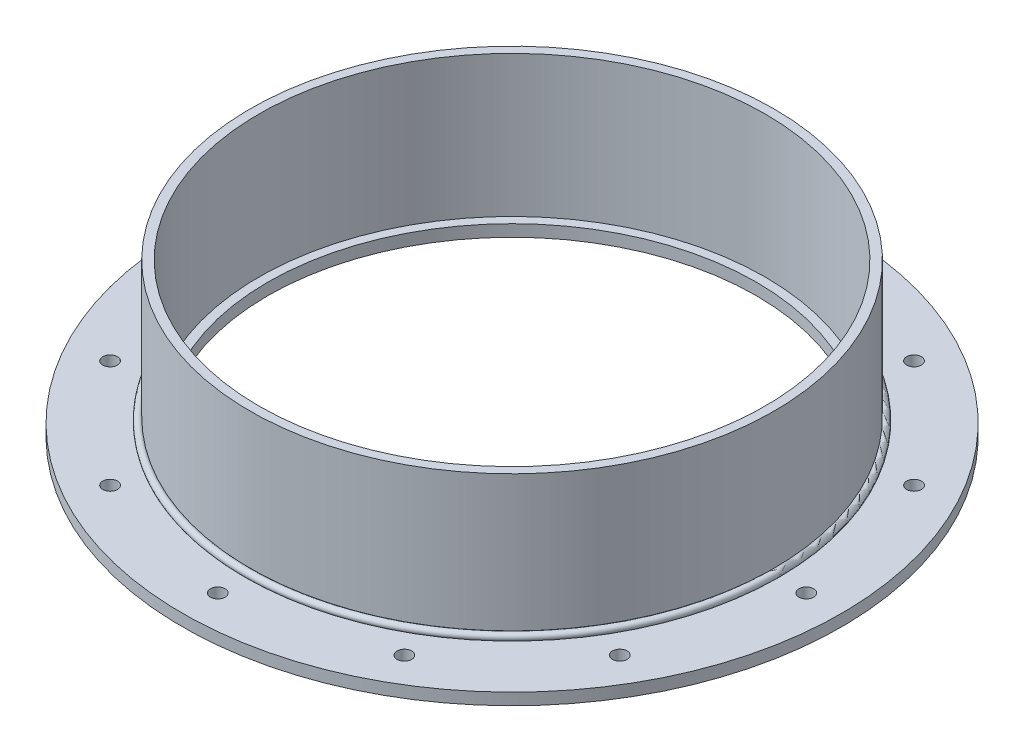
SolidWorks part; units mm, degrees
ref_plane "Front" through (0, 0, 0) normal (0, 0, 1) x (1, 0, 0)
ref_plane "Top" through (0, 0, 0) normal (0, 1, 0) x (1, 0, 0)
ref_plane "Right" through (0, 0, 0) normal (1, 0, 0) x (0, 0, -1)
sketch "Sketch1" plane through (0, 0, 0) normal (0, 0, 1) x (1, 0, 0)
  line L0 (0, 0) -> (0, 26.292) construction
  line L1 (-131.7625, 0) -> (-177.8, 0)
  line L2 (-131.7625, 0) -> (-131.7625, 6.35)
  line L3 (-131.7625, 6.35) -> (-177.8, 6.35)
  line L4 (-177.8, 0) -> (-177.8, 6.35)
  dimension "D1" = 6.35
  dimension "D2" = 355.6
  dimension "D3" = 263.525
revolve "Revolve1" add sketch "Sketch1" angle 360 about L0
sketch "Sketch2" plane through (0, 0, 0) normal (0, 0, 1) x (1, 0, 0)
  line L0 (177.8, 6.35) -> (-177.8, 6.35) construction
  line L1 (-141.2875, 6.35) -> (-136.525, 6.35)
  line L2 (-141.2875, 6.35) -> (-141.2875, 82.55)
  line L3 (-141.2875, 82.55) -> (-136.525, 82.55)
  line L4 (-136.525, 6.35) -> (-136.525, 82.55)
  line L5 (0, 0) -> (0, 56.4767) construction
  line L6 (-177.8, 0) -> (177.8, 0) construction
  dimension "D1" = 4.7625
  dimension "D2" = 273.05
  dimension "D3" = 82.55
revolve "Revolve2" add sketch "Sketch2" angle 360 about L5
sketch "Sketch3" plane through (0, 0, 0) normal (0, 0, 1) x (1, 0, 0)
  line L0 (-142.5109, 7.5734) -> (-141.2875, 6.35) construction
  line L1 (177.8, 6.35) -> (-177.8, 6.35) construction
  line L2 (-141.2875, 6.35) -> (-144.0733, 6.35)
  line L3 (-141.2875, 82.55) -> (-141.2875, 6.35) construction
  line L4 (-141.2875, 9.1358) -> (-141.2875, 6.35)
  line L5 (0, 0) -> (0, 19.0297) construction
  arc A0 (-141.2875, 9.1358) -> (-144.0733, 6.35) centre (-142.5109, 7.5734) ccw
  dimension "D1" = 3.9688
  dimension "D2" = 45
  dimension "D3" = 2.7858
revolve "Revolve3" add sketch "Sketch3" angle 360 about L5
sketch "Sketch4" plane through (0, 6.35, 0) normal (0, 1, 0) x (1, 0, 0)
  circle A0 centre (0, 158.75) radius 3.9687
  circle A1 centre (0, 0) radius 158.75 construction
  dimension "D1" = 317.5
  dimension "D2" = 7.9375
extrude "Cut-Extrude1" cut sketch "Sketch4" against normal through all
pattern_circular "CirPattern1" count 12 over 360 about axis through (0, 0, 0) along (0, 1, 0) of "Cut-Extrude1"
